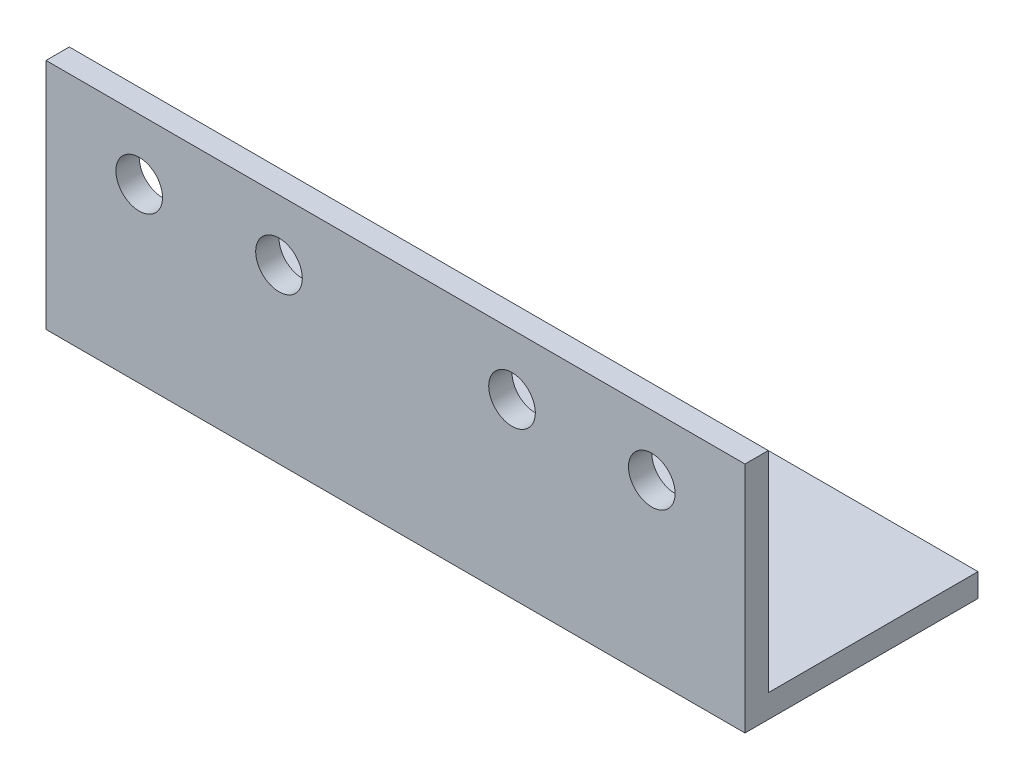
SolidWorks part; units mm, degrees
ref_plane "Спереди" through (0, 0, 0) normal (0, 0, 1) x (1, 0, 0)
ref_plane "Сверху" through (0, 0, 0) normal (0, 1, 0) x (1, 0, 0)
ref_plane "Справа" through (0, 0, 0) normal (1, 0, 0) x (0, 0, -1)
sketch "Эскиз1" plane through (0, 0, 0) normal (1, 0, 0) x (0, 0, -1)
  line L0 (0, 0) -> (0, 50)
  line L1 (0, 0) -> (50, 0)
extrude "Вытянуть-Тонкостенный1" add sketch "Эскиз1" along normal blind 150 thin
sketch "Эскиз2" plane through (0, 0, 0) normal (0, 0, 1) x (1, 0, 0)
  line L0 (75, 57.1198) -> (75, 24.9932) construction
  circle A0 centre (20, 37) radius 5
  circle A1 centre (50, 37) radius 5
  circle A2 centre (100, 37) radius 5
  circle A3 centre (130, 37) radius 5
  dimension "D1" = 2
extrude "Вырез-Вытянуть1" cut sketch "Эскиз2" against normal through all
sketch "Эскиз3" plane through (0, 0, 0) normal (0, -1, 0) x (1, 0, 0)
  line L0 (75, -55.6806) -> (75, -1.3862) construction
  circle A0 centre (130, -18) radius 5
  circle A1 centre (100, -18) radius 5
  circle A2 centre (50, -18) radius 5
  circle A3 centre (20, -18) radius 5
  dimension "D1" = 2
extrude "Вырез-Вытянуть2" cut sketch "Эскиз3" against normal through all
